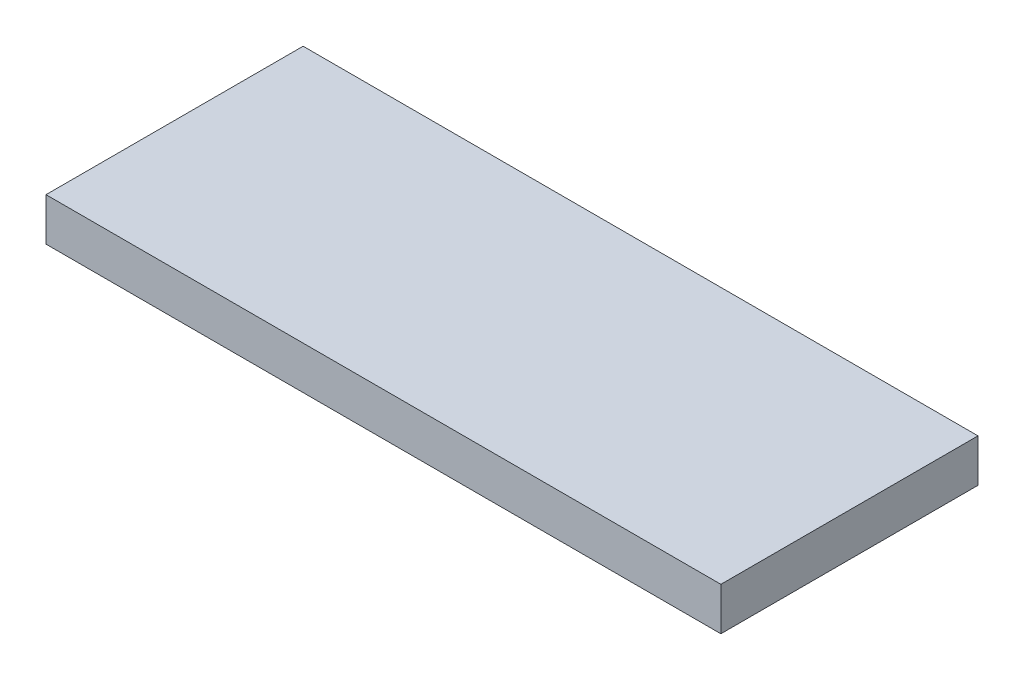
SolidWorks part; units mm, degrees
ref_plane "Front Plane" through (0, 0, 0) normal (0, 0, 1) x (1, 0, 0)
ref_plane "Top Plane" through (0, 0, 0) normal (0, 1, 0) x (1, 0, 0)
ref_plane "Right Plane" through (0, 0, 0) normal (1, 0, 0) x (0, 0, -1)
sketch "Sketch1" plane through (0, 0, 0) normal (0, 1, 0) x (1, 0, 0)
  line L0 (0, 0) -> (57.48, 0) construction
  line L10 (-21.26, -19.05) -> (78.74, -19.05)
  line L11 (-21.26, -19.05) -> (-21.26, 19.05)
  line L12 (-21.26, 19.05) -> (78.74, 19.05)
  line L13 (78.74, -19.05) -> (78.74, 19.05)
  line L14 (-21.26, -19.05) -> (78.74, 19.05) construction
  line L15 (-21.26, 19.05) -> (78.74, -19.05) construction
  circle A0 centre (0, 0) radius 2.54
  circle A1 centre (57.48, 0) radius 2.54
  point P4 (28.74, 0)
  dimension "D2" = 5.08
  dimension "D1" = 57.48
  dimension "D3" = 38.1
  dimension "D4" = 100
extrude "Boss-Extrude1" add sketch "Sketch1" along normal blind 6.35
sketch "Sketch2" plane through (0, 6.35, 0) normal (0, 1, 0) x (1, 0, 0)
  line L1 (-21.26, 19.05) -> (78.74, 19.05)
  line L2 (-21.26, 19.05) -> (-21.26, -19.05)
  line L3 (-21.26, -19.05) -> (78.74, -19.05)
  line L4 (78.74, 19.05) -> (78.74, -19.05)
extrude "Boss-Extrude2" add sketch "Sketch2" against normal blind 2.54
